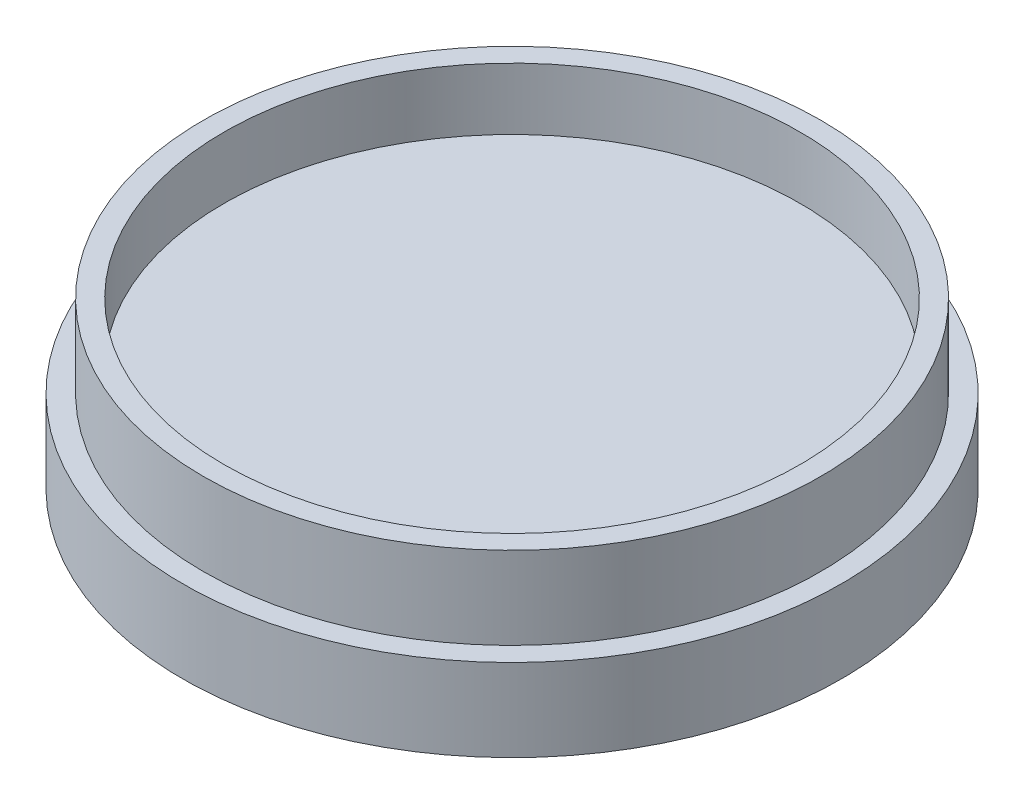
SolidWorks part; units mm, degrees
ref_plane "Front Plane" through (0, 0, 0) normal (0, 0, 1) x (1, 0, 0)
ref_plane "Top Plane" through (0, 0, 0) normal (0, 1, 0) x (1, 0, 0)
ref_plane "Right Plane" through (0, 0, 0) normal (1, 0, 0) x (0, 0, -1)
sketch "Sketch1" plane through (0, 0, 0) normal (0, 1, 0) x (1, 0, 0)
  circle A0 centre (0, 0) radius 95.15
extrude "Boss-Extrude1" add sketch "Sketch1" along normal blind 25.4
sketch "Sketch2" plane through (0, 25.4, 0) normal (0, 1, 0) x (1, 0, 0)
  circle A0 centre (0, 0) radius 88.8
extrude "Cut-Extrude1" cut sketch "Sketch2" against normal blind 19.05
sketch "Sketch3" plane through (0, 0, 0) normal (0, -1, 0) x (1, 0, 0)
  circle A0 centre (0, 0) radius 101.6
extrude "Boss-Extrude2" add sketch "Sketch3" along normal blind 25.4
sketch "Sketch4" plane through (0, -25.4, 0) normal (0, -1, 0) x (1, 0, 0)
  circle A0 centre (0, 82.55) radius 12.827
  circle A2 centre (78.5097, 25.5094) radius 12.827
  circle A3 centre (48.5217, -66.7844) radius 12.827
  circle A4 centre (-48.5217, -66.7844) radius 12.827
  circle A5 centre (-78.5097, 25.5094) radius 12.827
  point P15 (0, 0)
  dimension "D1" = 82.55
  dimension "D2" = 25.654
  dimension "D3" = 5
extrude "Cut-Extrude2" cut sketch "Sketch4" against normal blind 19.05
